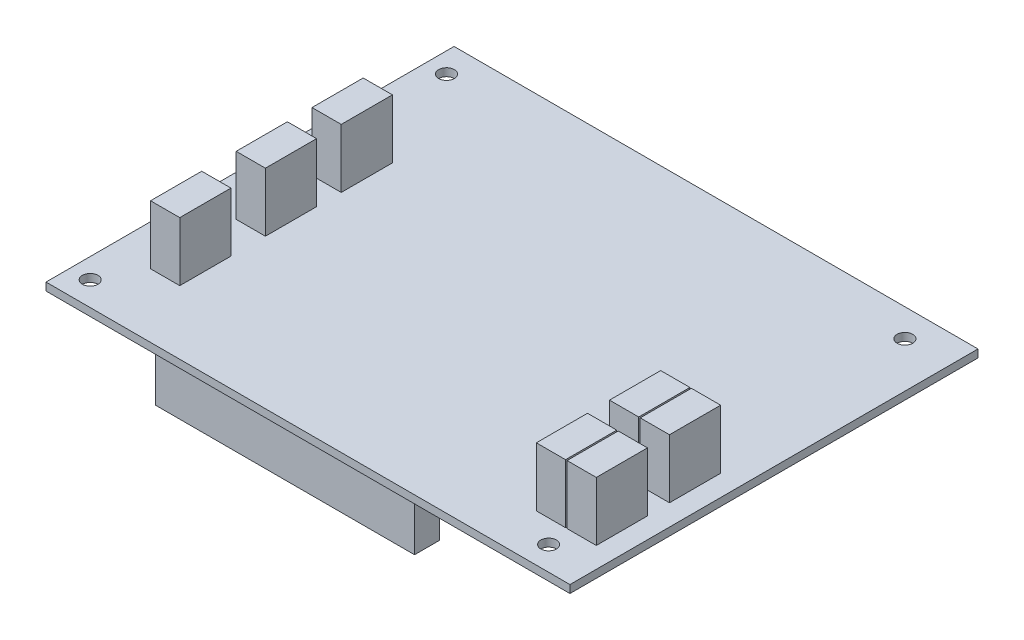
SolidWorks part; units mm, degrees
ref_plane "Plan de face" through (0, 0, 0) normal (0, 0, 1) x (1, 0, 0)
ref_plane "Plan de dessus" through (0, 0, 0) normal (0, 1, 0) x (1, 0, 0)
ref_plane "Plan de droite" through (0, 0, 0) normal (1, 0, 0) x (0, 0, -1)
sketch "Esquisse1" plane through (0, 0, 0) normal (0, 1, 0) x (1, 0, 0)
  line L1 (-21, -3.5) -> (83, -3.5)
  line L2 (-21, -3.5) -> (-21, 77.5)
  line L3 (-21, 77.5) -> (83, 77.5)
  line L4 (83, -3.5) -> (83, 77.5)
  circle A0 centre (-17, 1.27) radius 1.55
  circle A1 centre (-17, 72) radius 1.55
  circle A2 centre (74, 72) radius 1.55
  circle A3 centre (74, 1.27) radius 1.55
  dimension "D5" = 3.1
  dimension "D6" = 3.1
  dimension "D7" = 3.1
  dimension "D8" = 3.1
  dimension "D1" = 21
  dimension "D2" = 3.5
  dimension "D3" = 81
  dimension "D4" = 104
extrude "Extrusion2" add sketch "Esquisse1" along normal blind 1.55
sketch "Esquisse2" plane through (0, 1.55, 0) normal (0, 1, 0) x (-1, 0, 0)
  line L1 (1.6, -74.475) -> (-49.86, -74.475)
  line L2 (1.6, -74.475) -> (1.6, -69.525)
  line L3 (1.6, -69.525) -> (-49.86, -69.525)
  line L4 (-49.86, -74.475) -> (-49.86, -69.525)
  line L5 (1.6, -3.745) -> (-49.86, -3.745)
  line L6 (1.6, -3.745) -> (1.6, 1.205)
  line L7 (1.6, 1.205) -> (-49.86, 1.205)
  line L8 (-49.86, -3.745) -> (-49.86, 1.205)
  circle A0 centre (17, -72) radius 1.55 construction
  circle A1 centre (17, -1.27) radius 1.55 construction
  dimension "D1" = 51.46
  dimension "D2" = 4.95
  dimension "D3" = 2.475
  dimension "D4" = 1.6
  dimension "D5" = 51.46
  dimension "D6" = 4.95
  dimension "D7" = 2.475
  dimension "D8" = 1.6
extrude "Extrusion3" add sketch "Esquisse2" against normal blind 12.6
sketch "Esquisse3" plane through (0, 1.55, 0) normal (0, 1, 0) x (-1, 0, 0)
  line L0 (12.9, -36.31) -> (7.1, -36.31)
  line L1 (12.9, -19.31) -> (7.1, -19.31)
  line L2 (12.9, -19.31) -> (12.9, -9.15)
  line L3 (12.9, -9.15) -> (7.1, -9.15)
  line L4 (7.1, -19.31) -> (7.1, -9.15)
  line L5 (12.9, -36.31) -> (12.9, -26.15)
  line L6 (12.9, -26.15) -> (7.1, -26.15)
  line L7 (7.1, -36.31) -> (7.1, -26.15)
  line L8 (12.9, -51.362) -> (7.1, -51.362)
  line L9 (12.9, -51.362) -> (12.9, -41.202)
  line L10 (12.9, -41.202) -> (7.1, -41.202)
  line L11 (7.1, -51.362) -> (7.1, -41.202)
  dimension "D1" = 10.16
  dimension "D2" = 5.8
  dimension "D3" = 7.1
  dimension "D4" = 9.15
  dimension "D5" = 7.1
  dimension "D6" = 10.16
  dimension "D7" = 26.15
  dimension "D8" = 7.1
  dimension "D9" = 41.202
  dimension "D10" = 10.16
  dimension "D11" = 5.8
extrude "Extrusion4" add sketch "Esquisse3" along normal blind 11.7
sketch "Esquisse4" plane through (0, 1.55, 0) normal (0, 1, 0) x (-1, 0, 0)
  line L1 (-67, -15.99) -> (-72.8, -15.99)
  line L2 (-67, -15.99) -> (-67, -5.83)
  line L3 (-67, -5.83) -> (-72.8, -5.83)
  line L4 (-72.8, -15.99) -> (-72.8, -5.83)
  line L5 (-73.1, -15.99) -> (-78.9, -15.99)
  line L6 (-73.1, -15.99) -> (-73.1, -5.83)
  line L7 (-73.1, -5.83) -> (-78.9, -5.83)
  line L8 (-78.9, -15.99) -> (-78.9, -5.83)
  line L9 (-66.9251, -30.59) -> (-72.7251, -30.59)
  line L10 (-66.9251, -30.59) -> (-66.9251, -20.43)
  line L11 (-66.9251, -20.43) -> (-72.7251, -20.43)
  line L12 (-72.7251, -30.59) -> (-72.7251, -20.43)
  line L13 (-73.0251, -30.59) -> (-78.8251, -30.59)
  line L14 (-73.0251, -30.59) -> (-73.0251, -20.43)
  line L15 (-73.0251, -20.43) -> (-78.8251, -20.43)
  line L16 (-78.8251, -30.59) -> (-78.8251, -20.43)
  dimension "D1" = 10.16
  dimension "D2" = 5.8
  dimension "D3" = 67
  dimension "D4" = 5.83
  dimension "D5" = 73.1
  dimension "D6" = 5.83
  dimension "D7" = 10.16
  dimension "D8" = 5.8
  dimension "D9" = 20.43
  dimension "D10" = 20.43
extrude "Extrusion5" add sketch "Esquisse4" along normal blind 11.7
